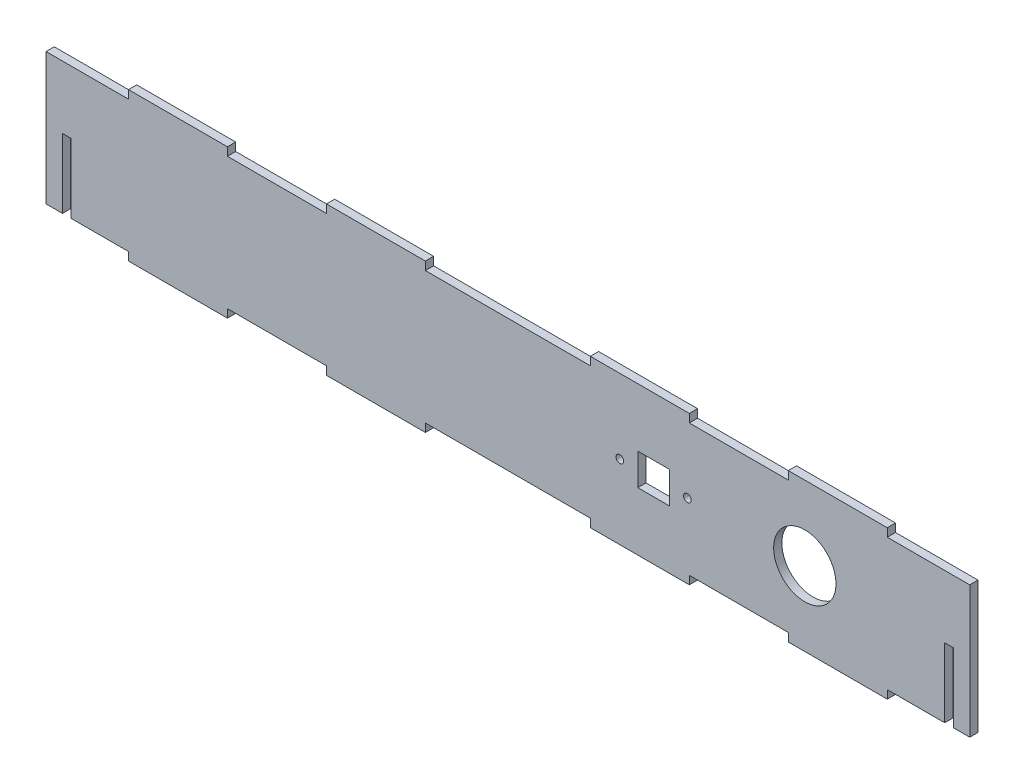
SolidWorks part; units mm, degrees
ref_plane "Front Plane" through (0, 0, 0) normal (0, 0, 1) x (1, 0, 0)
ref_plane "Top Plane" through (0, 0, 0) normal (0, 1, 0) x (1, 0, 0)
ref_plane "Right Plane" through (0, 0, 0) normal (1, 0, 0) x (0, 0, -1)
sketch "Sketch1" plane through (0, 0, 0) normal (0, 0, 1) x (1, 0, 0)
  line L1 (0, 50.8) -> (355.6, 50.8)
  line L2 (0, 50.8) -> (0, 0)
  line L3 (0, 0) -> (355.6, 0)
  line L4 (355.6, 50.8) -> (355.6, 0)
  dimension "D1" = 50.8
  dimension "D2" = 355.6
extrude "Boss-Extrude1" add sketch "Sketch1" along normal blind 3.175
ref_plane "Plane1" through (177.8, 0, 0) normal (-1, 0, 0) x (0, 0, 1)
ref_plane "Plane2" through (0, 25.4, 0) normal (0, 1, 0) x (1, 0, 0)
sketch "Sketch2" plane through (0, 50.8, 0) normal (0, 1, 0) x (1, 0, 0)
  line L0 (-55, 0) -> (55, 0) construction
  line L1 (31.75, 0) -> (69.85, 0)
  line L2 (31.75, 0) -> (31.75, -3.175)
  line L3 (31.75, -3.175) -> (69.85, -3.175)
  line L4 (69.85, 0) -> (69.85, -3.175)
  line L5 (355.6, 0) -> (0, 0) construction
  line L6 (107.95, 0) -> (146.05, 0)
  line L7 (107.95, 0) -> (107.95, -3.175)
  line L8 (107.95, -3.175) -> (146.05, -3.175)
  line L9 (146.05, 0) -> (146.05, -3.175)
  line L10 (355.6, -3.175) -> (0, -3.175) construction
  line L11 (50.8, -3.175) -> (50.8, 0) construction
  line L12 (127, -3.175) -> (127, 0) construction
  line L13 (177.8, 1.7463) -> (177.8, -1.7463) construction
  dimension "D1" = 76.2
  dimension "D2" = 50.8
  dimension "D3" = 38.1
extrude "Boss-Extrude2" add sketch "Sketch2" along normal blind 3.175
mirror "Mirror1" about plane through (177.8, 0, 0) normal (-1, 0, 0) of "Boss-Extrude2"
mirror "Mirror2" about plane through (0, 25.4, 0) normal (0, 1, 0) of "Mirror1", "Boss-Extrude2"
sketch "Sketch3" plane through (0, 0, 0) normal (0, 0, -1) x (-1, 0, 0)
  line L0 (0, 1.7463) -> (0, -1.7463) construction
  line L1 (-6.35, 0) -> (-9.652, 0)
  line L2 (-6.35, 0) -> (-6.35, 26.67)
  line L3 (-6.35, 26.67) -> (-9.652, 26.67)
  line L4 (-9.652, 0) -> (-9.652, 26.67)
  line L5 (1.7463, 0) -> (-1.7463, 0) construction
  point P6 (-8.001, 0)
  dimension "D1" = 3.302
  dimension "D2" = 6.35
  dimension "D3" = 26.67
extrude "Cut-Extrude1" cut sketch "Sketch3" against normal blind 3.175
mirror "Mirror3" about plane through (177.8, 0, 0) normal (-1, 0, 0) of "Cut-Extrude1"
sketch "Sketch4" plane through (0, 0, 0) normal (0, 0, -1) x (-1, 0, 0)
  line L0 (-246.9, 25.4) -> (-220.9, 25.4) construction
  line L1 (-215.9, 19.15) -> (-251.9, 19.15) construction
  line L2 (-215.9, 19.15) -> (-215.9, 31.65) construction
  line L3 (-215.9, 31.65) -> (-251.9, 31.65) construction
  line L4 (-251.9, 19.15) -> (-251.9, 31.65) construction
  line L5 (-215.9, 19.15) -> (-251.9, 31.65) construction
  line L6 (-215.9, 31.65) -> (-251.9, 19.15) construction
  line L7 (-209.55, 50.8) -> (-146.05, 50.8) construction
  line L8 (-227.804, 19.304) -> (-239.996, 19.304)
  line L9 (-227.804, 19.304) -> (-227.804, 31.496)
  line L10 (-227.804, 31.496) -> (-239.996, 31.496)
  line L11 (-239.996, 19.304) -> (-239.996, 31.496)
  line L12 (-227.804, 19.304) -> (-239.996, 31.496) construction
  line L13 (-227.804, 31.496) -> (-239.996, 19.304) construction
  line L14 (-177.8, -1.7463) -> (-177.8, 1.7463) construction
  line L15 (-355.6, 0) -> (-355.6, 50.8) construction
  circle A0 centre (-220.9, 25.4) radius 1.4732
  circle A1 centre (-246.9, 25.4) radius 1.4732
  circle A2 centre (-292.1, 25.4) radius 12
  point P0 (-233.9, 25.4)
  point P12 (-233.9, 25.4)
  point P13 (-233.9, 25.4)
  dimension "D5" = 24
  dimension "D9" = 2.9464
  dimension "D1" = 36
  dimension "D2" = 12.5
  dimension "D3" = 26
  dimension "D4" = 12.192
  dimension "D6" = 25.4
  dimension "D7" = 38.1
  dimension "D8" = 63.5
extrude "Cut-Extrude2" cut sketch "Sketch4" against normal through all both and the other way through all
equation "\"teeth\"= 1.5in'Teeth Width"
equation "\"D3@Sketch2\"=\"teeth\""
equation "\"t\"= 0.125in'Sheet Thicness"
equation "\"teeth_tol\"= 0.003in'Tolerance betwee Teeth"
